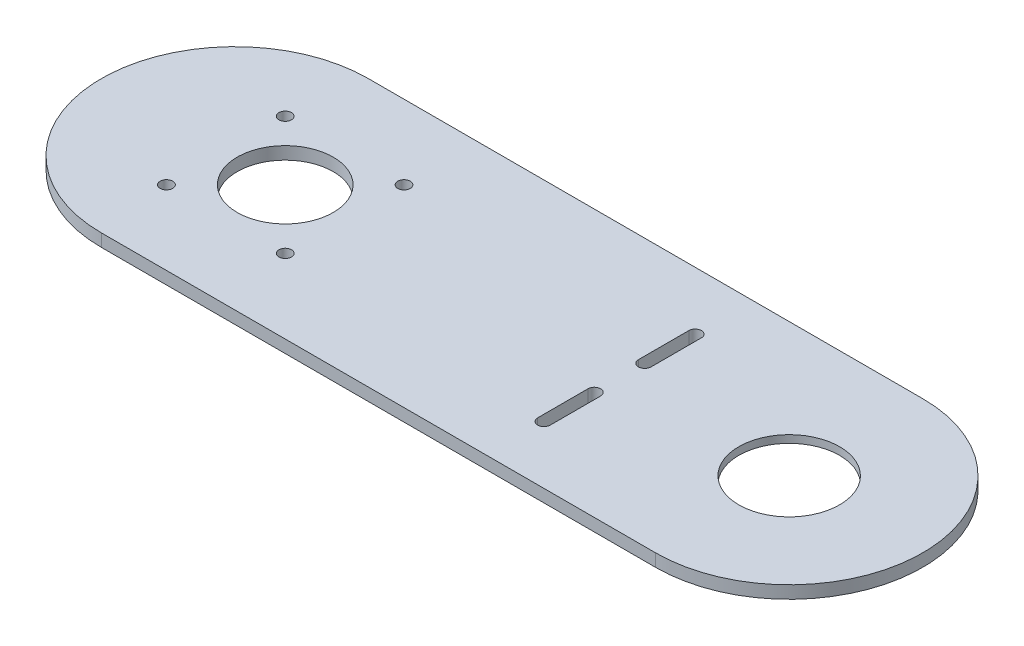
SolidWorks part; units mm, degrees
ref_plane "Front Plane" through (0, 0, 0) normal (0, 0, 1) x (1, 0, 0)
ref_plane "Top Plane" through (0, 0, 0) normal (0, 1, 0) x (1, 0, 0)
ref_plane "Right Plane" through (0, 0, 0) normal (1, 0, 0) x (0, 0, -1)
sketch "Sketch1" plane through (0, 0, 0) normal (0, 1, 0) x (1, 0, 0)
  line L1 (-110, -53) -> (110, -53)
  line L2 (-110, -53) -> (-110, 53)
  line L3 (-110, 53) -> (110, 53)
  line L4 (110, -53) -> (110, 53)
  line L5 (-110, -53) -> (110, 53) construction
  line L6 (-110, 53) -> (110, -53) construction
  circle A0 centre (-110, 0) radius 53
  circle A1 centre (110, 0) radius 53
  point P0 (0, 0)
  dimension "D1" = 220
  dimension "D2" = 106
extrude "Boss-Extrude1" add sketch "Sketch1" along normal blind 5 contours L2 A0 | L2 A0 | A1 L3 A0 L1 | L4 A1 | L4 A1
sketch "Sketch2" plane through (0, 5, 0) normal (0, 1, 0) x (1, 0, 0)
  circle A0 centre (110, 0) radius 20
  dimension "D1" = 40
extrude "Cut-Extrude1" cut sketch "Sketch2" against normal through all
sketch "Sketch3" plane through (0, 0, 0) normal (0, -1, 0) x (1, 0, 0)
  circle A0 centre (110, 0) radius 30
  dimension "D1" = 60
extrude "Cut-Extrude2" cut sketch "Sketch3" against normal blind 2
sketch "Sketch4" plane through (0, 5, 0) normal (0, 1, 0) x (1, 0, 0)
  line L0 (-163, 0) -> (0, 0) construction
  line L1 (0, 0) -> (90, 0) construction
  line L2 (-118.2, 28.2) -> (-61.8, 28.2) construction
  line L3 (-118.2, 28.2) -> (-118.2, -28.2) construction
  line L4 (-118.2, -28.2) -> (-61.8, -28.2) construction
  line L5 (-61.8, 28.2) -> (-61.8, -28.2) construction
  line L6 (-118.2, 28.2) -> (-61.8, -28.2) construction
  line L7 (-118.2, -28.2) -> (-61.8, 28.2) construction
  line L8 (-113.57, 23.57) -> (-66.43, 23.57) construction
  line L9 (-113.57, 23.57) -> (-113.57, -23.57) construction
  line L10 (-113.57, -23.57) -> (-66.43, -23.57) construction
  line L11 (-66.43, 23.57) -> (-66.43, -23.57) construction
  line L12 (-113.57, 23.57) -> (-66.43, -23.57) construction
  line L13 (-113.57, -23.57) -> (-66.43, 23.57) construction
  line L14 (45.1826, 10) -> (45.1826, 30)
  line L15 (40.1826, -10) -> (40.1826, -30)
  line L16 (45.1826, -10) -> (45.1826, -30)
  line L17 (40.1826, 10) -> (40.1826, 30)
  arc A0 (-110, 53) -> (-110, -53) centre (-110, 0) ccw construction
  circle A1 centre (-113.57, 23.57) radius 2.5
  circle A2 centre (-66.43, 23.57) radius 2.5
  circle A3 centre (-66.43, -23.57) radius 2.5
  circle A4 centre (-113.57, -23.57) radius 2.5
  circle A5 centre (-90, 0) radius 19.05
  circle A7 centre (110, 0) radius 20 construction
  arc A8 (45.1826, -10) -> (40.1826, -10) centre (42.6826, -10) ccw
  arc A9 (40.1826, -30) -> (45.1826, -30) centre (42.6826, -30) ccw
  arc A10 (40.1826, 30) -> (45.1826, 30) centre (42.6826, 30) cw
  arc A11 (45.1826, 10) -> (40.1826, 10) centre (42.6826, 10) cw
  point P6 (-90, 0)
  point P11 (-90, 0)
  point P24 (40.1826, -20)
  dimension "D1" = 5
  dimension "D2" = 38.1
  dimension "D8" = 20
  dimension "D9" = 5
  dimension "D3" = 56.4
  dimension "D4" = 56.4
  dimension "D5" = 47.14
  dimension "D6" = 200
  dimension "D7" = 20
extrude "Cut-Extrude3" cut sketch "Sketch4" against normal through all
